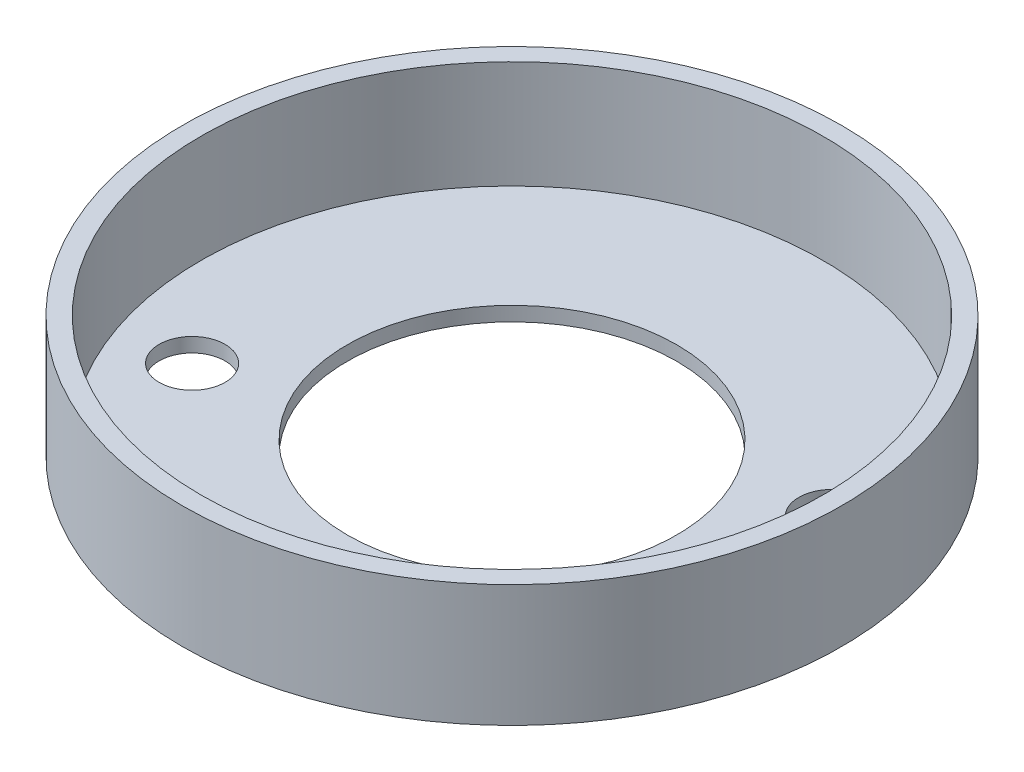
SolidWorks part; units mm, degrees
ref_plane "Front Plane" through (0, 0, 0) normal (0, 0, 1) x (1, 0, 0)
ref_plane "Top Plane" through (0, 0, 0) normal (0, 1, 0) x (1, 0, 0)
ref_plane "Right Plane" through (0, 0, 0) normal (1, 0, 0) x (0, 0, -1)
sketch "Sketch1" plane through (0, 0, 0) normal (0, 1, 0) x (1, 0, 0)
  line L0 (0, 0) -> (-5.3351, 12.8805) construction
  line L1 (24.0182, 9.948) -> (-24.0238, -9.9508) construction
  line L2 (0, 0) -> (-12.31, 5.0992) construction
  circle A0 centre (0, 0) radius 17.5
  circle A1 centre (-24.0238, -9.9508) radius 3.5
  circle A3 centre (24.0182, 9.948) radius 3.5
  circle A4 centre (0, 0) radius 35
  circle A5 centre (9.951, -24.0242) radius 3.5
  dimension "D2" = 70
  dimension "D3" = 35
  dimension "D7" = 45
extrude "Boss-Extrude1" add sketch "Sketch1" along normal blind 12.954
sketch "Sketch2" plane through (0, 12.954, 0) normal (0, 1, 0) x (1, 0, 0)
  circle A0 centre (0, 0) radius 33.02
  dimension "D1" = 66.04
extrude "Cut-Extrude1" cut sketch "Sketch2" against normal blind 11.43
